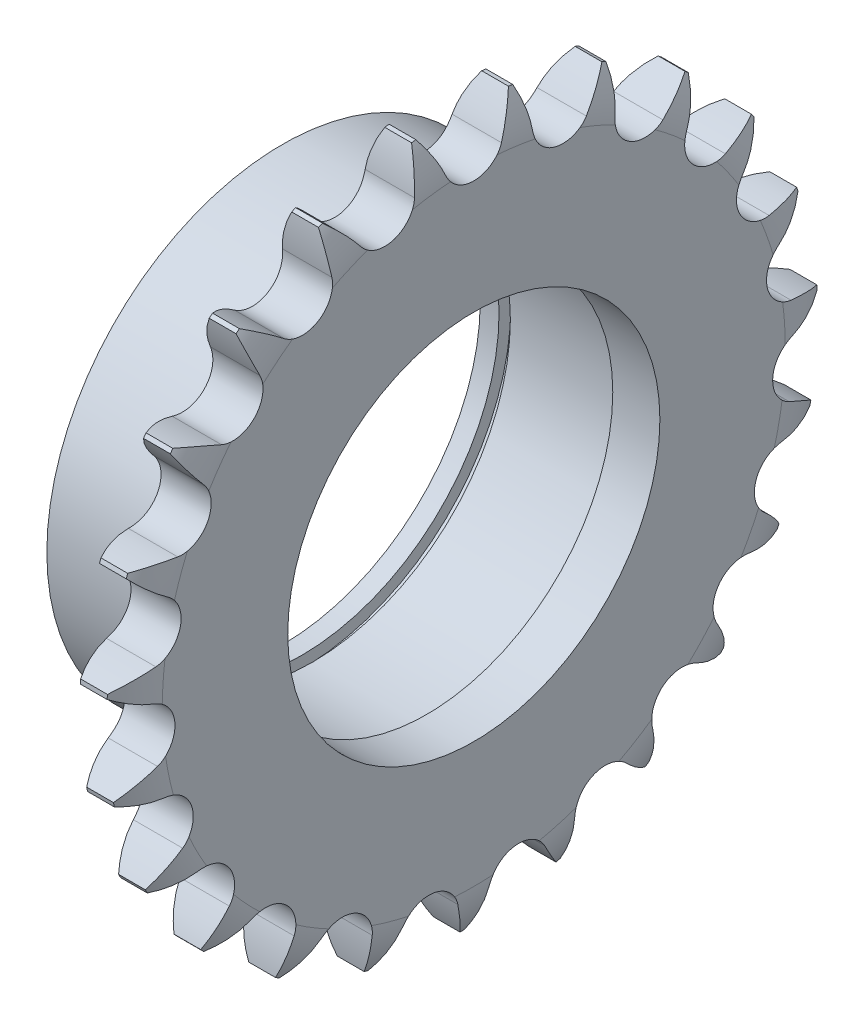
SolidWorks part; units mm, degrees
ref_plane "Plane1" through (0, 0, 0) normal (0, 0, 1) x (1, 0, 0)
ref_plane "Plane2" through (0, 0, 0) normal (0, 1, 0) x (1, 0, 0)
ref_plane "Plane3" through (0, 0, 0) normal (1, 0, 0) x (0, 0, -1)
sketch "Clipboard" plane through (0, 0, 0) normal (0, 1, 0) x (1, 0, 0)
  line L0 (0, 0) -> (8.7678, -3.7217)
  line L1 (-15, 0) -> (100, 0) construction
  line L2 (0, 0) -> (-0.8203, 0.9272)
  line L3 (0, 0) -> (-8.8973, 3.4006)
  line L4 (0, 0) -> (2.8536, 1.2113)
  line L5 (0, 0) -> (-15.9282, -5.9407)
  line L6 (0, 0) -> (-4.4098, -2.9753)
  line L7 (-0.8203, 0.9272) -> (14.7104, 7.8419)
  line L8 (-76.2, 38.1) -> (-72.9, 38.1)
  line L9 (-73.3242, 40.7328) -> (-72.926, 40.7699)
  line L10 (-73.4529, 9.1872) -> (-63.2129, 9.1872)
  circle A0 centre (0, 0) radius 3.175
  circle A1 centre (0, 0) radius 25
  circle A2 centre (0, 0) radius 25
  dimension "Dr" = 6.35
  dimension "MHD" = 50
  dimension "Hub_dia" = 50
  dimension "Num_teeth" = 23
  dimension "Pitch" = 9.525
  dimension "Width" = 3.1
  dimension "Side_relief" = 1.238
  dimension "Side_radius" = 9.525
  dimension "Overall_len" = 17
  dimension "Show_teeth" = 23
  dimension "Thickness" = 5.3196
  dimension "OAL" = 17.0005
  dimension "T_dim" = 3.3
  dimension "Fillet_rad" = 0.4
  dimension "Face_width" = 5.32
  dimension "Num_strands" = 1
  dimension "Transv_pitch" = 10.24
  dimension "Plate_wid" = 8.26
sketch "BasProSke" plane through (0, 0, 0) normal (0, 1, 0) x (1, 0, 0)
  line L0 (-10, 0) -> (60, 0) construction
  line L1 (0, 0) -> (0, 33.0578)
  line L2 (0, 0) -> (5.3196, 0)
  line L3 (5.3196, 0) -> (5.3196, 33.0578)
  line L4 (4.0816, 37.7536) -> (1.238, 37.7536)
  arc A0 (0, 33.0578) -> (1.238, 37.7536) centre (9.525, 33.0578) cw
  arc A1 (5.3196, 33.0578) -> (4.0816, 37.7536) centre (-4.2054, 33.0578) ccw
  dimension "Thickness" = 5.3196
  dimension "D1" = 9.525
  dimension "G1" = 1.238
  dimension "G2" = 1.238
  dimension "Diameter" = 75.5073
revolve "Base-Revolve" add sketch "BasProSke" angle 360 about L0
sketch "TooCutSke" plane through (0, 0, 0) normal (1, 0, 0) x (0, 0, -1)
  line L0 (0, 35.0073) -> (2.9742, 33.8083) construction
  line L1 (0, 0) -> (0, 107) construction
  line L2 (0, 35.0073) -> (-10, 35.0073) construction
  line L3 (0, 35.0073) -> (-2.9742, 33.8083) construction
  arc A0 (2.9742, 33.8083) -> (5.2383, 37.8933) centre (20.6424, 26.6854) cw
  arc A1 (2.9742, 33.8083) -> (-2.9742, 33.8083) centre (0, 35.0073) cw
  arc A2 (-2.9742, 33.8083) -> (-5.2383, 37.8933) centre (-20.6424, 26.6854) ccw
  arc A3 (5.2383, 37.8933) -> (-5.2383, 37.8933) centre (0, 0) ccw
  dimension "R1" = 3.2067
  dimension "R2" = 19.05
  dimension "Overcut" = 38.2536
  dimension "Seat_radius" = 35.0073
  dimension "X" = 136.087
extrude "ToothCut" cut sketch "TooCutSke" along normal through all
pattern_circular "TeethCuts" count 23 every 15.652 about axis through (-10, 0, 0) along (1, 0, 0) of "ToothCut"
sketch "HubNeaOneSke" plane through (0, 0, 0) normal (-1, 0, 0) x (0, 0, 1)
  circle A0 centre (0, 0) radius 25
  dimension "Diameter" = 50
extrude "HubNearOne" add sketch "HubNeaOneSke" along normal blind 15
fillet "HubNearOneFillet" radius 0.4 1 edges at (0, 0, -25)
sketch "HubNeaBotSke" plane through (0, 0, 0) normal (-1, 0, 0) x (0, 0, 1)
  circle A0 centre (0, 0) radius 25
  dimension "Diameter" = 50
extrude "HubNearBoth" [suppressed] add sketch "HubNeaBotSke" along normal blind 5.8404
fillet "HubNearBothFillet" [suppressed] radius 0.4
ref_plane "FarPln" through (5.3196, 0, 0) normal (1, 0, 0) x (0, 0, -1)
sketch "HubFarSke" plane through (5.3196, 0, 0) normal (1, 0, 0) x (0, 0, -1)
  circle A0 centre (0, 0) radius 25
  dimension "Diameter" = 50
extrude "HubFar" [suppressed] add sketch "HubFarSke" along normal blind 5.8404
fillet "HubFarFillet" [suppressed] radius 0.4
sketch "BorSke" plane through (0, 0, 0) normal (1, 0, 0) x (0, 0, -1)
  circle A0 centre (0, 0) radius 21
  dimension "Diameter" = 42
extrude "Bore" cut sketch "BorSke" along normal mid plane 34.001
sketch "KeySke" plane through (0, 0, 0) normal (1, 0, 0) x (0, 0, -1)
  line L0 (-6, 0) -> (-6, 24.3)
  line L1 (-6, 24.3) -> (6, 24.3)
  line L2 (6, 24.3) -> (6, 0)
  line L3 (0, 0) -> (0, 34) construction
  line L4 (-6, 0) -> (6, 0)
  dimension "Offset" = 24.3
  dimension "Width" = 12
extrude "Keyway" [suppressed] cut sketch "KeySke" along normal mid plane 34.001
pattern_circular "Keyway2" [suppressed] count 2 every 90 about axis through (-10, 0, 0) along (1, 0, 0)
sketch "Sketch2" plane through (5.3196, 0, 0) normal (1, 0, 0) x (0, 0, -1)
  circle A0 centre (0, 0) radius 21
  circle A1 centre (0, 0) radius 19.75
extrude "Boss-Extrude1" add sketch "Sketch2" against normal blind 5
sketch "Sketch4" plane through (-15, 0, 0) normal (-1, 0, 0) x (0, 0, 1)
  circle A3 centre (0, 0) radius 22.25
  circle A4 centre (0, 0) radius 21
extrude "Cut-Extrude1" cut sketch "Sketch4" against normal blind 3.2
sketch "Sketch5" plane through (-15, 0, 0) normal (-1, 0, 0) x (0, 0, 1)
  circle A2 centre (0, 0) radius 22.25
  circle A3 centre (0, 0) radius 21
extrude "Boss-Extrude2" add sketch "Sketch5" against normal blind 2
equation "' \"Pitch@Clipboard\" = 12.7"
equation "' \"Num_strands@Clipboard\" = 1"
equation "' \"Num_teeth@Clipboard\" = 9"
equation "' \"Hub_dia@Clipboard\" = 50"
equation "' \"Overall_len@Clipboard\" = 3"
equation "' \"Diameter@BorSke\" = 12"
equation "' \"T_dim@Clipboard\" = 1"
equation "' \"Width@KeySke\" = 2"
equation "' \"Dr@Clipboard\" = 8.51"
equation "' \"Face_width@Clipboard\" = 7.2"
equation "' \"Side_radius@Clipboard\" = 12.7"
equation "' \"Side_relief@Clipboard\" = 1.27"
equation "' \"Transv_pitch@Clipboard\" = 13.92"
equation "' \"Show_teeth@Clipboard\" = 9"
equation "' \"Fillet_rad@Clipboard\" = 0.6"
equation "' \"Plate_wid@Clipboard\" = 11.8"
equation "\"Num_teeth@Clipboard\" = int( \"Num_teeth@Clipboard\" )"
equation "\"Num_teeth@Clipboard\" = ((sgn( \"Num_teeth@Clipboard\" - 5.0)+1)*( \"Num_teeth@Clipboard\" - 5.0))/2 +5.0"
equation "\"Num_teeth@Clipboard\" = ((sgn( \"Num_teeth@Clipboard\" - 200.0)-1)*( \"Num_teeth@Clipboard\" - 200.0))/-2 +200.0"
equation "\"MHD@Clipboard\" = \"Pitch@Clipboard\" * (1.0 / tan(3.14159265 / \"Num_teeth@Clipboard\" )) - 1.04 * \"Plate_wid@Clipboard\" - 0.76"
equation "\"Thickness@Clipboard\"  = \"Face_width@Clipboard\" + (\"Num_strands@Clipboard\" - 1) * \"Transv_pitch@Clipboard\""
equation "\"OAL@Clipboard\" = \"Thickness@Clipboard\" + 2 * \"Fillet_rad@Clipboard\" + 1"
equation "\"MHD@Clipboard\" = ((sgn( \"MHD@Clipboard\" - \"Hub_dia@Clipboard\" )-1)*( \"MHD@Clipboard\" - \"Hub_dia@Clipboard\" ))/-2+ \"Hub_dia@Clipboard\""
equation "\"OAL@Clipboard\" = ((sgn( \"OAL@Clipboard\" - \"Overall_len@Clipboard\" )+1)*( \"OAL@Clipboard\" - \"Overall_len@Clipboard\" ))/2 + \"Overall_len@Clipboard\" + 0.0005"
equation "\"Num_teeth@TeethCuts\" = int( \"Show_teeth@Clipboard\" ) + 1"
equation "\"Num_teeth@TeethCuts\" = ((sgn( \"Num_teeth@TeethCuts\" - \"Num_teeth@Clipboard\" )-1)*( \"Num_teeth@TeethCuts\" - \"Num_teeth@Clipboard\" ))/-2+ \"Num_teeth@Clipboard\""
equation "\"Num_teeth@TeethCuts\" = ((sgn( \"Num_teeth@TeethCuts\" - 2.0)+1)*( \"Num_teeth@TeethCuts\" - 2.0))/2 +2.0"
equation "\"Angle@TeethCuts\" = 360.0 / \"Num_teeth@Clipboard\""
equation "\"Seat_radius@TooCutSke\" = ( \"Pitch@Clipboard\" / 2.0) / sin(3.14159265 / \"Num_teeth@Clipboard\" ) - \"Dr@Clipboard\" / 2.0 + \"Dr@Clipboard\" * 0.505"
equation "\"R1@TooCutSke\"  = \"Dr@Clipboard\" * 0.505"
equation "\"X@TooCutSke\" = 140.0 - (90.0 / \"Num_teeth@Clipboard\")"
equation "\"R2@TooCutSke\" = 0.12 * \"Dr@Clipboard\" * ( \"Num_teeth@Clipboard\" + 2.0)"
equation "\"Overcut@TooCutSke\" = 0.5 + 0.625 * \"Pitch@Clipboard\" - 0.5 * \"Dr@Clipboard\"  +  \"Pitch@Clipboard\" / 2.0 / sin(3.14159265 / \"Num_teeth@Clipboard\" )"
equation "\"Diameter@BasProSke\" = 2.0 * ( 0.625 * \"Pitch@Clipboard\" - 0.5 * \"Dr@Clipboard\"  +  \"Pitch@Clipboard\" / 2.0 / sin(3.14159265 / \"Num_teeth@Clipboard\" ))"
equation "\"Thickness@BasProSke\"  = \"Thickness@Clipboard\""
equation "\"G1@BasProSke\" =  \"Side_relief@Clipboard\""
equation "\"G2@BasProSke\" =  \"Side_relief@Clipboard\""
equation "\"D1@BasProSke\" =  \"Side_radius@Clipboard\""
equation "\"Diameter@HubNeaOneSke\" = \"MHD@Clipboard\""
equation "\"Diameter@HubNeaBotSke\" = \"MHD@Clipboard\""
equation "\"Length@HubNearBoth\" = ( \"OAL@Clipboard\" - \"Thickness@BasProSke\" ) / 2.0"
equation "\"D1@HubNearOneFillet\" = \"Fillet_rad@Clipboard\""
equation "\"D1@HubNearBothFillet\" = \"Fillet_rad@Clipboard\""
equation "\"Thickness@FarPln\" = \"Thickness@BasProSke\""
equation "\"Diameter@HubFarSke\" = \"MHD@Clipboard\""
equation "\"Length@HubFar\" = ( \"OAL@Clipboard\" - \"Thickness@BasProSke\" ) / 2.0"
equation "\"D1@HubFarFillet\" = \"Fillet_rad@Clipboard\""
equation "\"D1@Bore\" = \"OAL@Clipboard\" * 2.0"
equation "\"D1@Keyway\" = \"OAL@Clipboard\" * 2.0"
equation "\"Offset@KeySke\" = \"T_dim@Clipboard\" + \"Diameter@BorSke\" / 2.0"
